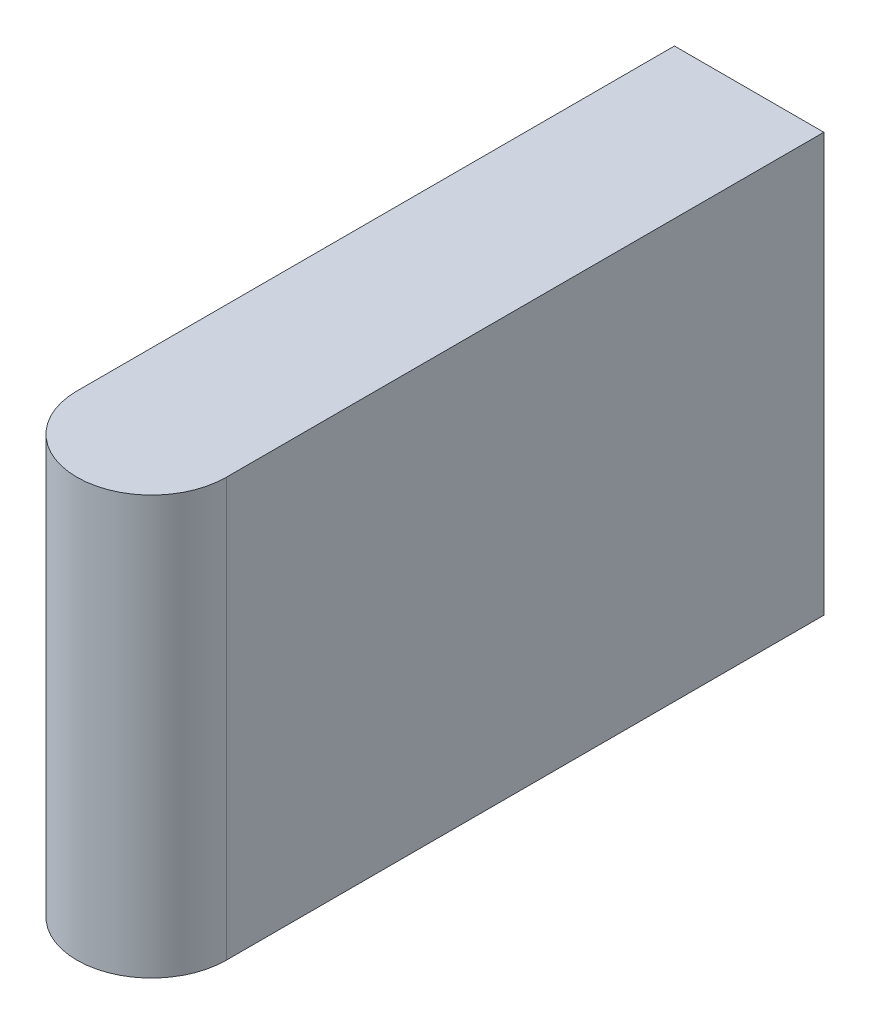
SolidWorks part; units mm, degrees
ref_plane "Face" through (0, 0, 0) normal (0, 0, 1) x (1, 0, 0)
ref_plane "Dessus" through (0, 0, 0) normal (0, 1, 0) x (1, 0, 0)
ref_plane "Droite" through (0, 0, 0) normal (1, 0, 0) x (0, 0, -1)
sketch "Esquisse1" plane through (0, 0, 0) normal (0, 1, 0) x (1, 0, 0)
  line L0 (0, 1.6762) -> (0, -5.3046) construction
  line L1 (0.5, 0) -> (0.5, -4)
  line L2 (-0.5, 0) -> (-0.5, -4)
  line L3 (-0.5, 0) -> (0.5, 0)
  arc A0 (-0.5, -4) -> (0.5, -4) centre (0, -4) ccw
  dimension "D2" = 4
  dimension "D1" = 1
extrude "Base-Extrusion" add sketch "Esquisse1" along normal mid plane 2.8
